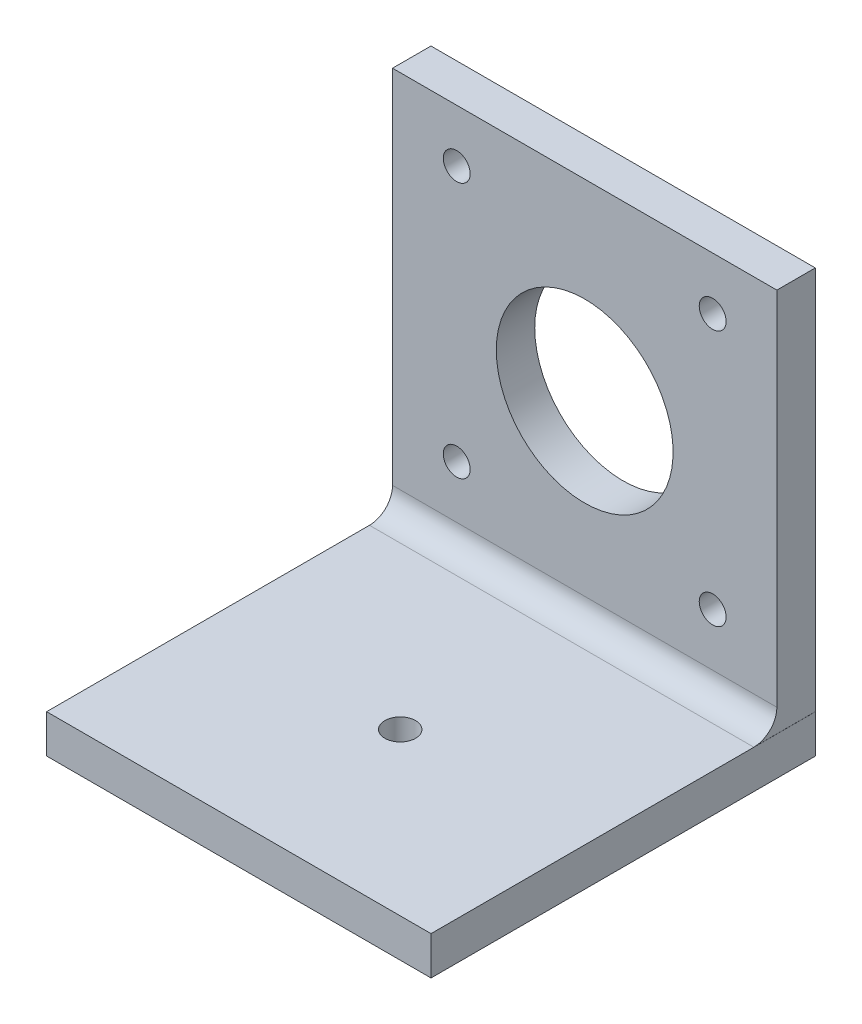
SolidWorks part; units mm, degrees
ref_plane "Plano frontal" through (0, 0, 0) normal (0, 0, 1) x (1, 0, 0)
ref_plane "Plano superior" through (0, 0, 0) normal (0, 1, 0) x (1, 0, 0)
ref_plane "Plano direito" through (0, 0, 0) normal (1, 0, 0) x (0, 0, -1)
sketch "Esboço1" plane through (0, 0, 0) normal (0, 0, 1) x (1, 0, 0)
  line L1 (0, 0) -> (50, 0)
  line L2 (0, 0) -> (0, 50)
  line L3 (0, 50) -> (50, 50)
  line L4 (50, 0) -> (50, 50)
  dimension "D1" = 50
  dimension "D2" = 50
extrude "Ressalto-extrusão1" add sketch "Esboço1" along normal blind 5
sketch "Esboço2" plane through (0, 0, 0) normal (0, 0, 1) x (1, 0, 0)
  line L1 (50, 0) -> (50, 50) construction
  circle A0 centre (25, 25) radius 11.5
  dimension "D1" = 23
extrude "Corte-extrusão1" cut sketch "Esboço2" along normal blind 8 and the other way blind 14
sketch "Esboço3" plane through (0, 0, 0) normal (0, 0, 1) x (1, 0, 0)
  line L1 (0, 0) -> (50.011, 0)
  line L2 (0, 0) -> (0, -5)
  line L3 (0, -5) -> (50.011, -5)
  line L4 (50.011, 0) -> (50.011, -5)
  dimension "D1" = 5
extrude "Ressalto-extrusão2" add sketch "Esboço3" along normal blind 50
fillet "Filete1" radius 3 1 edges
sketch "Esboço4" plane through (0, 0, 0) normal (0, 0, 1) x (1, 0, 0)
  line L0 (39.9, 43.15) -> (41.65, 43.15)
  line L1 (50, 3) -> (50, 50) construction
  line L3 (0, 3) -> (0, 26.5) construction
  line L4 (0, 50) -> (0, 3) construction
  line L5 (0, 26.5) -> (50, 26.5) construction
  line L7 (50, 50) -> (0, 50) construction
  line L8 (50, 50) -> (0, 50) construction
  line L10 (50, 0) -> (0, 0) construction
  circle A0 centre (8.35, 43.15) radius 1.75
  circle A1 centre (41.65, 43.15) radius 1.75
  circle A2 centre (41.65, 9.85) radius 1.75
  circle A3 centre (8.35, 9.85) radius 1.75
  point P0 (25, 50)
  point P14 (25, 50)
  point P17 (25, 50)
  point P22 (25, 0)
  dimension "D4" = 3.5
  dimension "D5" = 3.5
  dimension "D6" = 3.5
  dimension "D7" = 3.5
  dimension "D1" = 33.3
  dimension "D2" = 16.65
  dimension "D3" = 16.65
extrude "Corte-extrusão2" cut sketch "Esboço4" along normal blind 11 contours A3 | A0 | A1 | A2
sketch "Esboço5" plane through (0, 0, 0) normal (0, 1, 0) x (1, 0, 0)
  line L0 (25.0055, -50) -> (25, -8) construction
  line L1 (50.011, -50) -> (0, -50) construction
  line L2 (50, -8) -> (0, -8) construction
  line L3 (25, -8) -> (0, -8) construction
  line L4 (0, -8) -> (50.011, -50) construction
  circle A0 centre (25.0028, -29) radius 2
  dimension "D1" = 4
extrude "Corte-extrusão4" cut sketch "Esboço5" against normal blind 14
